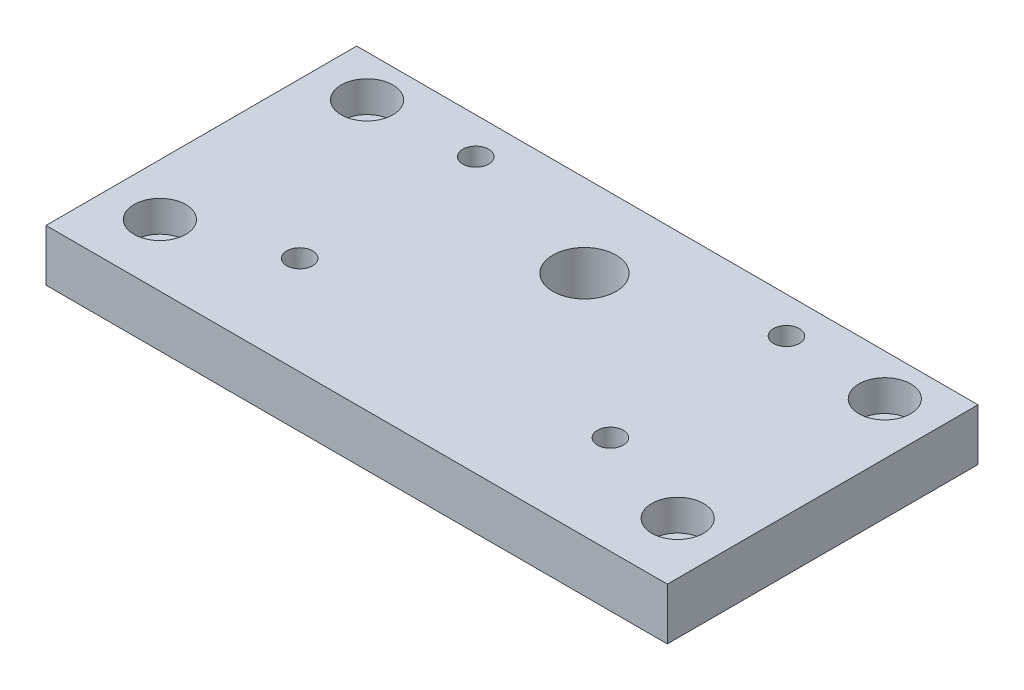
SolidWorks part; units mm, degrees
ref_plane "Front Plane" through (0, 0, 0) normal (0, 0, 1) x (1, 0, 0)
ref_plane "Top Plane" through (0, 0, 0) normal (0, 1, 0) x (1, 0, 0)
ref_plane "Right Plane" through (0, 0, 0) normal (1, 0, 0) x (0, 0, -1)
sketch "Sketch1" plane through (0, 0, 0) normal (0, 1, 0) x (1, 0, 0)
  line L1 (0, 0) -> (60, 0)
  line L2 (0, 0) -> (0, 30)
  line L3 (0, 30) -> (60, 30)
  line L4 (60, 0) -> (60, 30)
  dimension "D1" = 30
  dimension "D2" = 60
extrude "Boss-Extrude1" add sketch "Sketch1" along normal blind 5
sketch "Sketch2" plane through (0, 5, 0) normal (0, 1, 0) x (1, 0, 0)
  line L0 (60, 30) -> (0, 30) construction
  line L1 (60, 0) -> (60, 30) construction
  circle A0 centre (30, 22) radius 3.05
  circle A1 centre (45, 26.5) radius 1.25
  circle A2 centre (45, 9.5) radius 1.25
  dimension "D1" = 8
  dimension "D2" = 30
  dimension "D3" = 6.1
  dimension "D4" = 2.5
  dimension "D5" = 4.5
  dimension "D6" = 15
  dimension "D7" = 2.5
  dimension "D8" = 17
  dimension "D9" = 0
extrude "Cut-Extrude1" cut sketch "Sketch2" against normal blind 5
ref_plane "Plane1" through (30, 0, 0) normal (-1, 0, 0) x (0, 0, 1)
mirror "Mirror1" about plane through (30, 0, 0) normal (-1, 0, 0) of "Cut-Extrude1"
sketch "Sketch3" plane through (0, 5, 0) normal (0, 1, 0) x (1, 0, 0)
  circle A0 centre (55, 26) radius 1.25
  circle A1 centre (30, 22) radius 3.05 construction
  circle A2 centre (55, 6) radius 1.25
  dimension "D1" = 25
  dimension "D2" = 4
  dimension "D3" = 2.5
  dimension "D4" = 2.5
  dimension "D5" = 16
extrude "Cut-Extrude2" cut sketch "Sketch3" against normal blind 5
mirror "Mirror2" about plane through (30, 0, 0) normal (-1, 0, 0) of "Cut-Extrude2"
sketch "Sketch4" plane through (0, 5, 0) normal (0, 1, 0) x (1, 0, 0)
  circle A0 centre (55, 26) radius 2.5
  circle A1 centre (55, 6) radius 2.5
  dimension "D1" = 5
  dimension "D2" = 5
extrude "Cut-Extrude3" cut sketch "Sketch4" against normal blind 3
mirror "Mirror3" about plane through (30, 0, 0) normal (-1, 0, 0) of "Cut-Extrude3"
